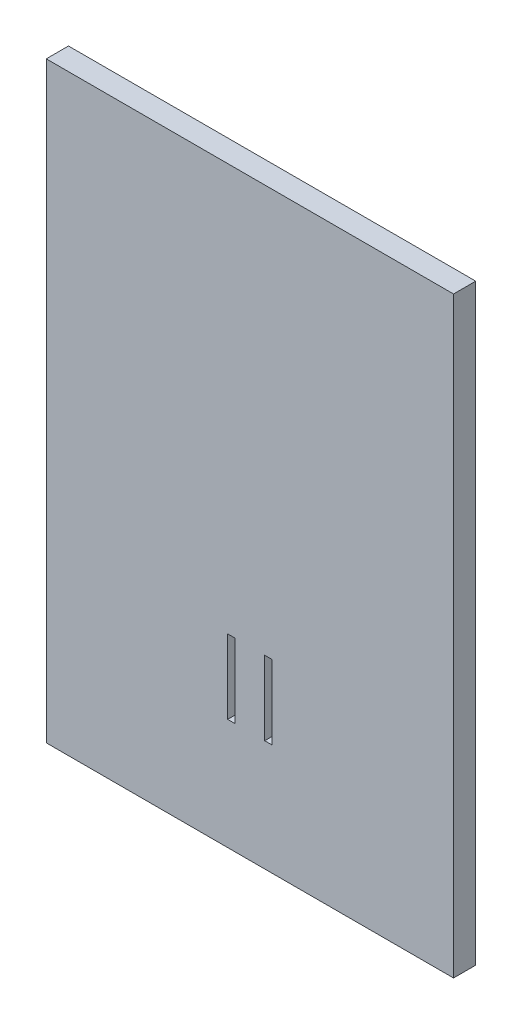
SolidWorks part; units mm, degrees
ref_plane "Front Plane" through (0, 0, 0) normal (0, 0, 1) x (1, 0, 0)
ref_plane "Top Plane" through (0, 0, 0) normal (0, 1, 0) x (1, 0, 0)
ref_plane "Right Plane" through (0, 0, 0) normal (1, 0, 0) x (0, 0, -1)
sketch "Sketch1" plane through (0, 0, 0) normal (0, 0, 1) x (1, 0, 0)
  line L1 (-27.5, 40) -> (27.5, 40)
  line L2 (-27.5, 40) -> (-27.5, -40)
  line L3 (-27.5, -40) -> (27.5, -40)
  line L4 (27.5, 40) -> (27.5, -40)
  line L5 (0, 40) -> (0, -15) construction
  line L6 (-2, -15) -> (2, -15) construction
  line L7 (2, -15) -> (3, -15)
  line L8 (2, -15) -> (2, -25)
  line L9 (2, -25) -> (3, -25)
  line L10 (3, -15) -> (3, -25)
  line L11 (-2, -15) -> (-3, -15)
  line L12 (-2, -15) -> (-2, -25)
  line L13 (-2, -25) -> (-3, -25)
  line L14 (-3, -15) -> (-3, -25)
  dimension "D1" = 55
  dimension "D2" = 80
  dimension "D3" = 55
  dimension "D4" = 2
  dimension "D5" = 10
  dimension "D6" = 1
extrude "Boss-Extrude1" add sketch "Sketch1" along normal blind 3
